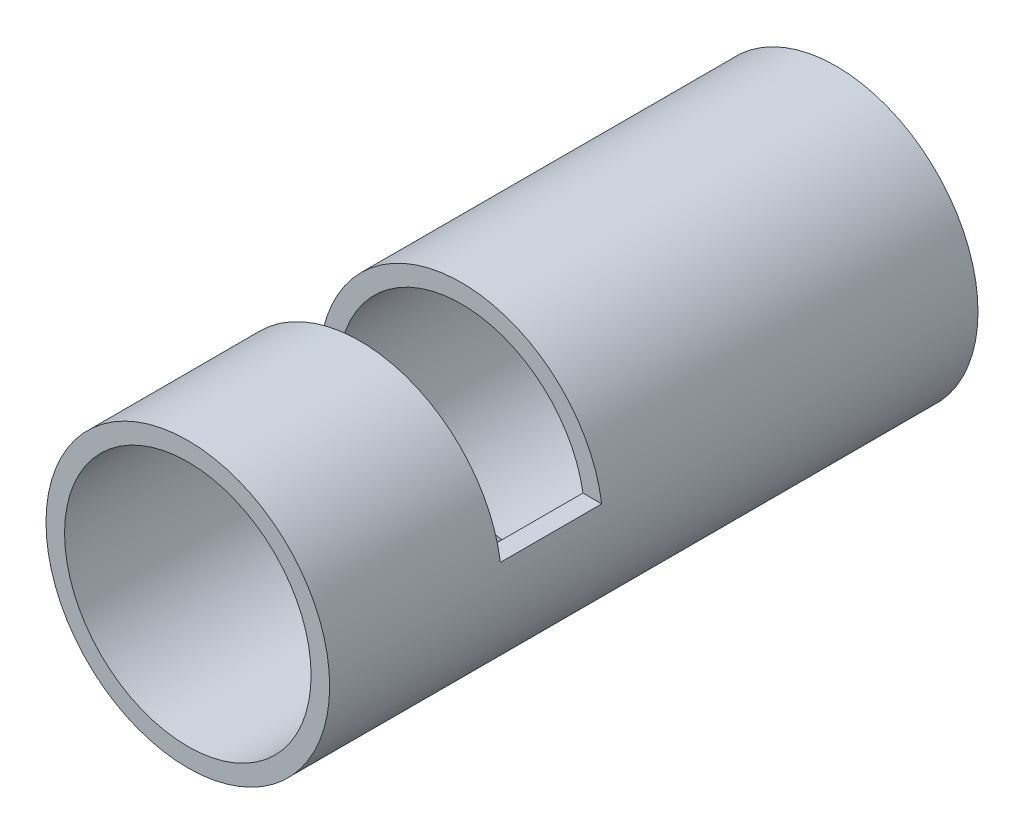
SolidWorks part; units mm, degrees
material "PVC Rigid"
ref_plane "Front Plane" through (0, 0, 0) normal (0, 0, 1) x (1, 0, 0)
ref_plane "Top Plane" through (0, 0, 0) normal (0, 1, 0) x (1, 0, 0)
ref_plane "Right Plane" through (0, 0, 0) normal (1, 0, 0) x (0, 0, -1)
sketch "Sketch1" plane through (0, 0, 0) normal (0, 0, 1) x (1, 0, 0)
  circle A0 centre (0, 0) radius 38.6334
  circle A1 centre (0, 0) radius 44.45
  dimension "D1" = 88.9
  dimension "D2" = 77.2668
extrude "base" add sketch "Sketch1" along normal blind 203.2
sketch "Sketch2" plane through (0, 0, 0) normal (1, 0, 0) x (0, 0, -1)
  line L0 (-203.2, 44.45) -> (-203.2, -44.45) construction
  line L1 (-203.2, 44.45) -> (-203.2, -44.45)
  line L2 (0, -44.45) -> (0, 44.45) construction
  line L3 (0, -44.45) -> (0, 44.45)
  line L4 (-203.2, 44.45) -> (0, 44.45)
  line L5 (-203.2, -44.45) -> (0, -44.45)
  line L7 (-149.225, 44.45) -> (-117.475, 44.45)
  line L8 (-149.225, 44.45) -> (-149.225, 6.35)
  line L9 (-149.225, 6.35) -> (-117.475, 6.35)
  line L10 (-117.475, 44.45) -> (-117.475, 6.35)
  dimension "D1" = 53.975
  dimension "D2" = 31.75
  dimension "D3" = 38.1
extrude "sanding cut" cut sketch "Sketch2" against normal through all both and the other way through all contours L10 L4 L8 L9
sketch "Sketch3" plane through (0, 0, 0) normal (1, 0, 0) x (0, 0, -1)
  line L0 (-203.2, 44.45) -> (-203.2, -44.45) construction
  line L1 (-203.2, 44.45) -> (-203.2, -44.45)
  line L2 (0, -44.45) -> (0, 44.45) construction
  line L3 (0, -44.45) -> (0, 44.45)
  line L4 (-203.2, -44.45) -> (0, -44.45)
  line L5 (-117.475, 44.45) -> (-117.475, 6.35) construction
  line L6 (-136.525, -44.45) -> (-98.425, -44.45)
  line L7 (-136.525, -44.45) -> (-136.525, -31.75)
  line L8 (-136.525, -31.75) -> (-98.425, -31.75)
  line L9 (-98.425, -44.45) -> (-98.425, -31.75)
  dimension "D1" = 12.7
  dimension "D2" = 38.1
  dimension "D3" = 19.05
extrude "servo cut" cut sketch "Sketch3" against normal through all both and the other way through all contours L4 L9 L8 L7
